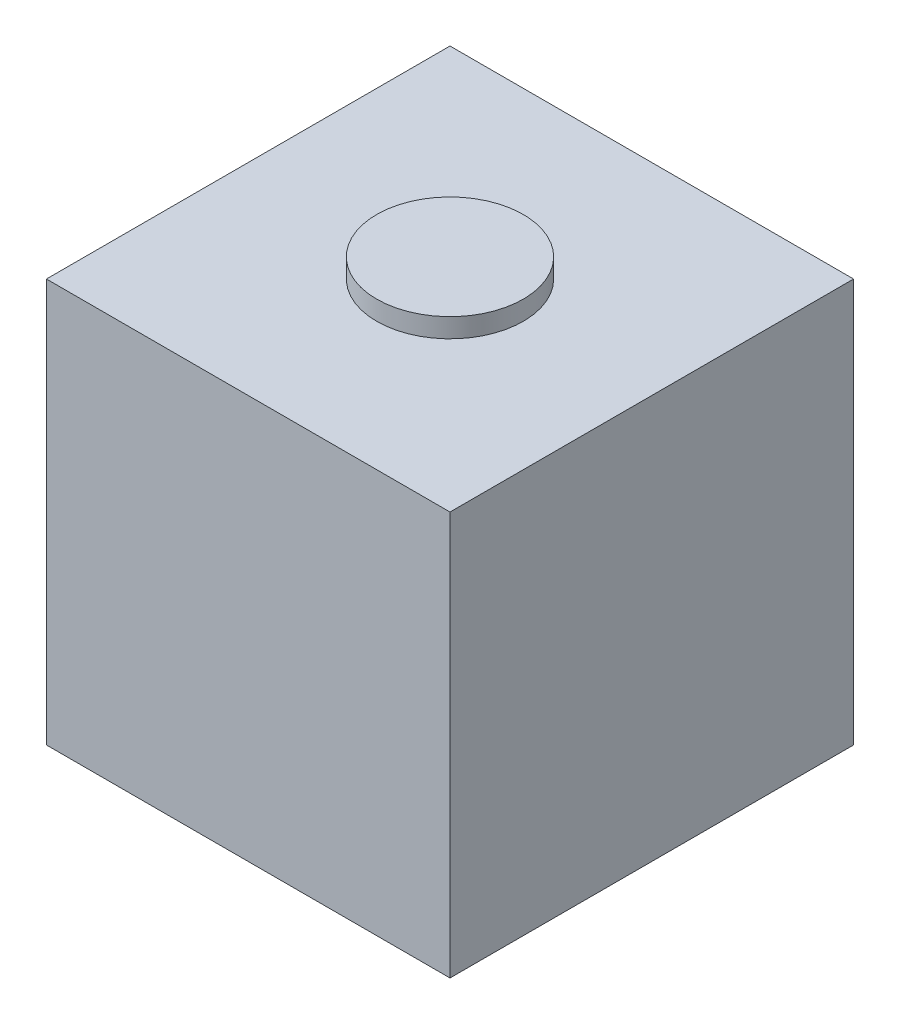
SolidWorks part; units mm, degrees
ref_plane "Front Plane" through (0, 0, 0) normal (0, 0, 1) x (1, 0, 0)
ref_plane "Top Plane" through (0, 0, 0) normal (0, 1, 0) x (1, 0, 0)
ref_plane "Right Plane" through (0, 0, 0) normal (1, 0, 0) x (0, 0, -1)
sketch "Sketch1" plane through (0, 0, 0) normal (0, 1, 0) x (1, 0, 0)
  line L1 (-21, -21) -> (21, -21)
  line L2 (-21, -21) -> (-21, 21)
  line L3 (-21, 21) -> (21, 21)
  line L4 (21, -21) -> (21, 21)
  line L5 (-21, -21) -> (21, 21) construction
  line L6 (-21, 21) -> (21, -21) construction
  point P0 (0, 0)
  dimension "D1" = 42
  dimension "D2" = 42
extrude "Boss-Extrude1" add sketch "Sketch1" along normal blind 42
sketch "Sketch2" plane through (0, 42, 0) normal (0, 1, 0) x (1, 0, 0)
  circle A0 centre (0, 0) radius 7.6309
extrude "Boss-Extrude2" add sketch "Sketch2" along normal blind 2
sketch "Sketch3" plane through (0, 44, 0) normal (0, 1, 0) x (1, 0, 0)
  circle A0 centre (0, 0) radius 3.2026
